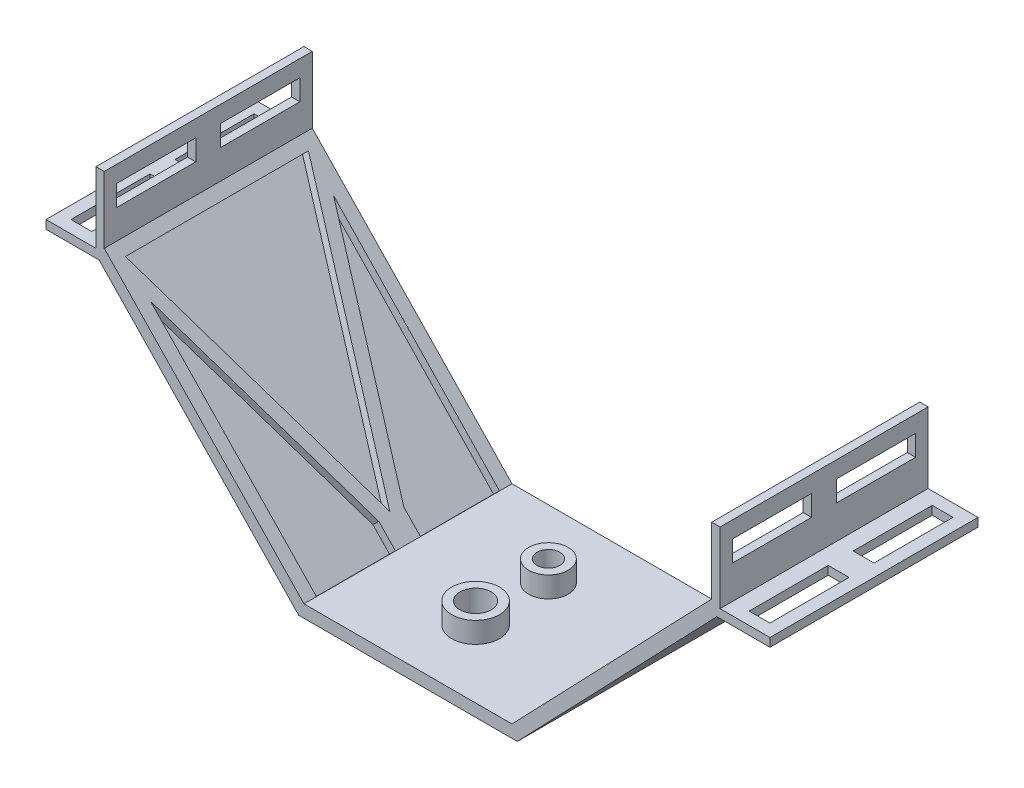
SolidWorks part; units mm, degrees
ref_plane "Front Plane" through (0, 0, 0) normal (0, 0, 1) x (1, 0, 0)
ref_plane "Top Plane" through (0, 0, 0) normal (0, 1, 0) x (1, 0, 0)
ref_plane "Right Plane" through (0, 0, 0) normal (1, 0, 0) x (0, 0, -1)
sketch "Sketch1" plane through (0, 0, 0) normal (0, 1, 0) x (1, 0, 0)
  line L0 (0, 17.5) -> (0, 0) construction
  line L2 (-25, 33.75) -> (25, 33.75)
  line L3 (-25, 33.75) -> (-25, -16.25)
  line L4 (-25, -16.25) -> (25, -16.25)
  line L5 (25, 33.75) -> (25, -16.25)
  circle A0 centre (0, 0) radius 3.75
  circle A1 centre (0, 17.5) radius 2.75
  point P9 (0, 8.75)
  dimension "D1" = 5.5
  dimension "D2" = 7.5
  dimension "D3" = 17.5
  dimension "D4" = 50
  dimension "D5" = 50
  dimension "D6" = 25
  dimension "D7" = 25
extrude "Boss-Extrude1" add sketch "Sketch1" along normal blind 3
sketch "Sketch2" plane through (0, 0, 16.25) normal (0, 0, 1) x (1, 0, 0)
  line L0 (-25, 0) -> (-26.2787, 0)
  line L1 (-26.2787, 0) -> (-74.2331, 49.9526)
  line L2 (-85, 49.9526) -> (-85, 52)
  line L3 (-85, 52) -> (-75, 52)
  line L4 (-75, 52) -> (-75, 62)
  line L5 (-75, 62) -> (-73, 62)
  line L6 (-73, 62) -> (-73, 53)
  line L7 (-73, 53) -> (-25, 3)
  line L9 (-74.2331, 49.9526) -> (-85, 49.9526)
  line L10 (-25, 3) -> (-25, 0) construction
  line L11 (-25, 3) -> (-25, 0)
  dimension "D1" = 3
  dimension "D2" = 50
  dimension "D3" = 2
  dimension "D4" = 10
  dimension "D5" = 10
extrude "Boss-Extrude2" add sketch "Sketch2" against normal blind 50
sketch "Sketch3" plane through (-11.5112, -11.0508, 0) normal (0.7214, 0.6925, 0) x (0, 0, -1)
  line L0 (8.75, 88.7884) -> (8.75, 19.4775) construction
  line L1 (33.75, 88.7884) -> (-16.25, 88.7884) construction
  line L2 (33.75, 19.4775) -> (-16.25, 19.4775) construction
  line L3 (-13.25, 85.7884) -> (30.75, 85.7884)
  line L4 (30.75, 85.7884) -> (8.75, 25.7884)
  line L5 (8.75, 25.7884) -> (-13.25, 85.7884)
  line L6 (-13.25, 85.7884) -> (-13.0633, 86.2093)
  line L7 (30.75, 77.0739) -> (11.75, 25.2557)
  line L8 (11.75, 25.2557) -> (11.75, 19.4775)
  line L9 (11.75, 19.4775) -> (30.75, 19.4775)
  line L10 (30.75, 19.4775) -> (30.75, 22.8979)
  line L11 (30.75, 77.0739) -> (30.75, 22.8979)
  line L12 (-13.25, 77.0739) -> (-13.25, 19.4775)
  line L13 (-13.25, 19.4775) -> (5.75, 19.4775)
  line L14 (5.75, 19.4775) -> (5.75, 25.2557)
  line L15 (5.75, 25.2557) -> (-13.25, 77.0739)
  line L16 (-16.25, 19.4775) -> (-16.25, 88.7884) construction
  line L17 (33.75, 19.4775) -> (33.75, 88.7884) construction
  line M2 (-16.25, 19.4775) -> (33.75, 19.4775)
  dimension "D1" = 3
  dimension "D2" = 3
  dimension "D3" = 3
  dimension "D4" = 3
  dimension "D5" = 3
  dimension "D6" = 60
  dimension "D7" = 3
  dimension "D8" = 3
  dimension "D9" = 3
extrude "Cut-Extrude2" cut sketch "Sketch3" against normal blind 2 contours L3 L0 L4 | L0 L3 L5 | L14 L15 L12 M2 | L11 L7 L8 L10 M2
ref_plane "Plane1" through (0, 0, 0) normal (1, 0, 0) x (0, 0, -1)
mirror "Mirror1" about plane through (0, 0, 0) normal (1, 0, 0) of "Cut-Extrude2", "Boss-Extrude2"
sketch "Sketch10" plane through (85, 0, 0) normal (1, 0, 0) x (0, 0, -1)
  line L1 (-16.25, 52) -> (33.75, 52)
  line L2 (-16.25, 52) -> (-16.25, 49.9526)
  line L3 (-16.25, 49.9526) -> (33.75, 49.9526)
  line L4 (33.75, 52) -> (33.75, 49.9526)
extrude "Boss-Extrude6" add sketch "Sketch10" along normal blind 2
sketch "Sketch11" plane through (0, 49.9526, 0) normal (0, -1, 0) x (-1, 0, 0)
  line L1 (-84, -13.25) -> (-79, -13.25)
  line L2 (-84, -13.25) -> (-84, 5.75)
  line L3 (-84, 30.75) -> (-79, 30.75)
  line L4 (-84, 5.75) -> (-79, 5.75)
  line L5 (-87, -16.25) -> (-74.2331, -16.25) construction
  line L6 (-87, 33.75) -> (-74.2331, 33.75) construction
  line L7 (-79, 5.75) -> (-79, -13.25)
  line L8 (-84, 11.75) -> (-84, 30.75)
  line L9 (-84, 11.75) -> (-79, 11.75)
  line L10 (-79, 11.75) -> (-79, 30.75)
  line L11 (-87, 8.75) -> (-74.2331, 8.75) construction
  line L12 (-87, -16.25) -> (-87, 33.75) construction
  line L13 (-74.2331, 33.75) -> (-74.2331, -16.25) construction
  point P8 (-80.6166, 33.75)
  dimension "D1" = 5
  dimension "D2" = 3
  dimension "D3" = 3
  dimension "D4" = 3
  dimension "D5" = 3
extrude "Cut-Extrude4" cut sketch "Sketch11" against normal blind 4
mirror "Mirror2" about plane through (0, 0, 0) normal (1, 0, 0) of "Boss-Extrude6", "Cut-Extrude4"
sketch "Sketch12" plane through (0, 62, 0) normal (0, 1, 0) x (1, 0, 0)
  line L1 (75, -16.25) -> (73, -16.25)
  line L2 (75, -16.25) -> (75, 33.75)
  line L3 (75, 33.75) -> (73, 33.75)
  line L4 (73, -16.25) -> (73, 33.75)
  line L5 (-73, -16.25) -> (-75, -16.25)
  line L6 (-73, -16.25) -> (-73, 33.75)
  line L7 (-73, 33.75) -> (-75, 33.75)
  line L8 (-75, -16.25) -> (-75, 33.75)
extrude "Boss-Extrude7" add sketch "Sketch12" along normal blind 10
sketch "Sketch13" plane through (73, 0, 0) normal (-1, 0, 0) x (0, 0, 1)
  line L0 (-33.75, 62.5) -> (16.25, 62.5) construction
  line L1 (-33.75, 53) -> (-33.75, 72) construction
  line L2 (16.25, 53) -> (16.25, 72) construction
  line L3 (-8.75, 72) -> (-8.75, 53) construction
  line L4 (-33.75, 72) -> (16.25, 72) construction
  line L5 (-33.75, 53) -> (16.25, 53) construction
  line L7 (-30.75, 65) -> (-11.75, 65)
  line L8 (-30.75, 65) -> (-30.75, 60)
  line L9 (-30.75, 60) -> (-11.75, 60)
  line L10 (-11.75, 65) -> (-11.75, 60)
  line L11 (-5.75, 65) -> (13.25, 65)
  line L12 (-5.75, 65) -> (-5.75, 60)
  line L13 (-5.75, 60) -> (13.25, 60)
  line L14 (13.25, 65) -> (13.25, 60)
  dimension "D1" = 5
  dimension "D2" = 5
  dimension "D3" = 3
  dimension "D4" = 3
  dimension "D5" = 3
  dimension "D6" = 3
  dimension "D7" = 2.5
  dimension "D8" = 2.5
extrude "Cut-Extrude5" cut sketch "Sketch13" against normal blind 10
mirror "Mirror3" about plane through (0, 0, 0) normal (1, 0, 0) of "Cut-Extrude5"
sketch "Sketch14" plane through (0, 3, 0) normal (0, 1, 0) x (1, 0, 0)
  circle A0 centre (0, 0) radius 3.75
  circle A1 centre (0, 0) radius 5.75
  circle A2 centre (0, 17.5) radius 2.75
  circle A3 centre (0, 17.5) radius 4.75
  dimension "D1" = 2
  dimension "D2" = 2
extrude "Boss-Extrude8" add sketch "Sketch14" along normal blind 5
sketch "Sketch15" plane through (73, 0, 0) normal (-1, 0, 0) x (0, 0, 1)
  line L0 (16.25, 53) -> (16.25, 72) construction
  line L1 (-33.75, 72) -> (16.25, 72)
  line L2 (-33.75, 72) -> (-33.75, 69)
  line L3 (-33.75, 69) -> (16.25, 69)
  line L4 (16.25, 72) -> (16.25, 69)
  dimension "D1" = 3
extrude "Cut-Extrude6" cut sketch "Sketch15" against normal through all both and the other way through all
